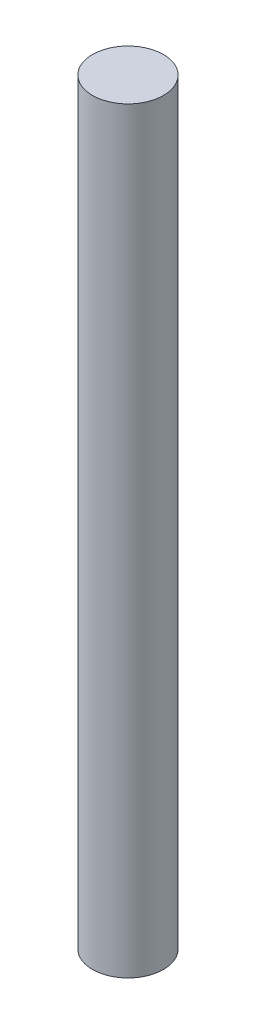
SolidWorks part; units mm, degrees
ref_plane "Front Plane" through (0, 0, 0) normal (0, 0, 1) x (1, 0, 0)
ref_plane "Top Plane" through (0, 0, 0) normal (0, 1, 0) x (1, 0, 0)
ref_plane "Right Plane" through (0, 0, 0) normal (1, 0, 0) x (0, 0, -1)
sketch "Sketch1" plane through (0, 0, 0) normal (0, 1, 0) x (1, 0, 0)
  circle A0 centre (0, 0) radius 2.3813
  dimension "D1" = 4.7625
extrude "Boss-Extrude1" add sketch "Sketch1" along normal blind 50.8 contours A0
